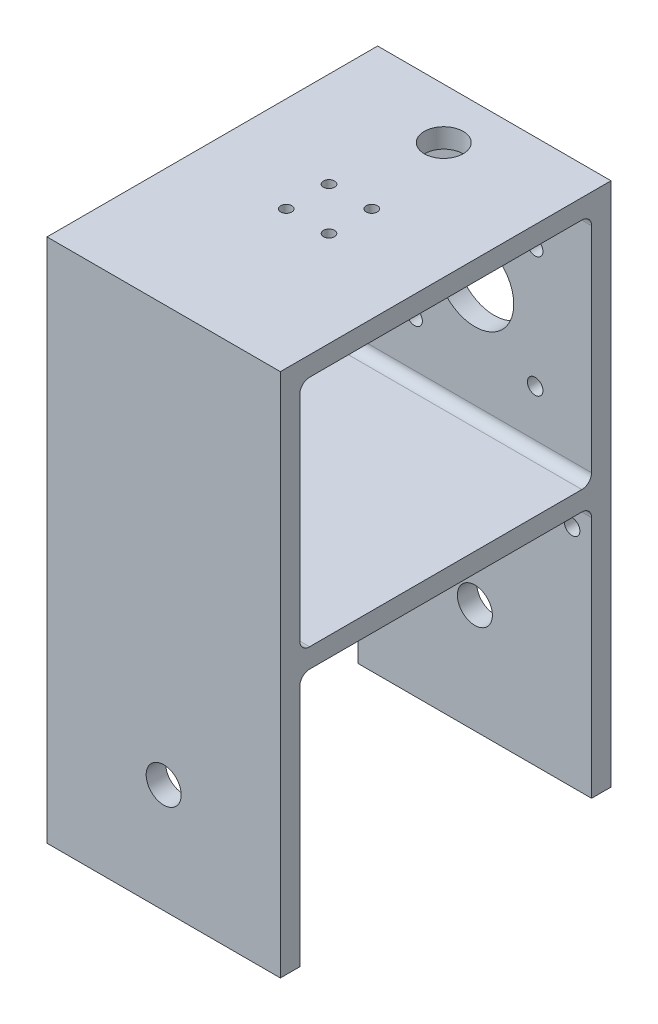
SolidWorks part; units mm, degrees
ref_plane "Front Plane" through (0, 0, 0) normal (0, 0, 1) x (1, 0, 0)
ref_plane "Top Plane" through (0, 0, 0) normal (0, 1, 0) x (1, 0, 0)
ref_plane "Right Plane" through (0, 0, 0) normal (1, 0, 0) x (0, 0, -1)
sketch "Sketch1" plane through (0, 0, 0) normal (1, 0, 0) x (0, 0, -1)
  line L0 (0, 0) -> (0, -135)
  line L1 (0, -135) -> (-5, -135)
  line L2 (-5, -135) -> (-5, -70)
  line L3 (-5, -70) -> (-80, -70)
  line L4 (-80, -70) -> (-80, -135)
  line L5 (-80, -135) -> (-85, -135)
  line L6 (-85, -135) -> (-85, 0)
  line L7 (-85, 0) -> (0, 0)
  dimension "D1" = 85
  dimension "D2" = 5
  dimension "D3" = 5
  dimension "D4" = 75
  dimension "D5" = 65
  dimension "D6" = 65
  dimension "D7" = 70
  dimension "D8" = 135
extrude "Boss-Extrude1" add sketch "Sketch1" against normal blind 60
sketch "Sketch2" plane through (0, 0, 0) normal (1, 0, 0) x (0, 0, -1)
  line L0 (-80, -70) -> (-5, -70) construction
  line L1 (-80, -65) -> (-5, -65)
  line L2 (-80, -65) -> (-80, -5)
  line L3 (-80, -5) -> (-5, -5)
  line L4 (-5, -65) -> (-5, -5)
  line L5 (0, 0) -> (-85, 0) construction
  line L6 (0, -135) -> (0, 0) construction
  line L7 (-85, 0) -> (-85, -135) construction
  dimension "D1" = 5
  dimension "D2" = 5
  dimension "D3" = 5
  dimension "D4" = 5
  dimension "D5" = 60
extrude "Cut-Extrude1" cut sketch "Sketch2" against normal blind 60
sketch "Sketch3" plane through (0, 0, 0) normal (0, 1, 0) x (1, 0, 0)
  line L0 (-30, 0) -> (-30, -85) construction
  line L1 (-60, 0) -> (0, 0) construction
  line L2 (-60, -85) -> (0, -85) construction
  line L3 (-60, -42.5) -> (0, -42.5) construction
  line L4 (-60, 0) -> (-60, -85) construction
  line L5 (0, 0) -> (0, -85) construction
  circle A0 centre (-35.5, -37) radius 1.425
  circle A1 centre (-24.5, -37) radius 1.425
  circle A2 centre (-24.5, -48) radius 1.425
  circle A3 centre (-35.5, -48) radius 1.425
  circle A4 centre (-30, -13) radius 5
  dimension "D5" = 2.85
  dimension "D6" = 2.85
  dimension "D7" = 2.85
  dimension "D8" = 2.85
  dimension "D9" = 10
  dimension "D1" = 11
  dimension "D2" = 11
  dimension "D3" = 24.5
  dimension "D4" = 37
  dimension "D10" = 13
extrude "Cut-Extrude2" cut sketch "Sketch3" against normal up to next
sketch "Sketch4" plane through (0, 0, 0) normal (0, 0, 1) x (1, 0, 0)
  line L0 (-30, 0) -> (-30, -135) construction
  line L1 (-60, 0) -> (0, 0) construction
  line L2 (-60, -135) -> (0, -135) construction
  line L3 (-60, 0) -> (0, 0) construction
  line L4 (0, 0) -> (0, -135) construction
  line L5 (-60, 0) -> (-60, -135) construction
  line L6 (-60, -135) -> (0, -135) construction
  line L11 (0, -67.5) -> (-60, -67.5) construction
  line L12 (0, -135) -> (0, 0) construction
  line L13 (-60, -135) -> (-60, 0) construction
  circle A0 centre (-30, -107) radius 4.5
  circle A1 centre (-30, -35) radius 10
  circle A6 centre (-5, -77) radius 2
  circle A7 centre (-55, -77) radius 2
  circle A8 centre (-14.5, -19.5) radius 2
  circle A9 centre (-45.5, -19.5) radius 2
  circle A10 centre (-45.5, -50.5) radius 2
  circle A11 centre (-14.5, -50.5) radius 2
  dimension "D2" = 9
  dimension "D3" = 20
  dimension "D7" = 4
  dimension "D8" = 4
  dimension "D9" = 4
  dimension "D10" = 4
  dimension "D19" = 4
  dimension "D20" = 4
  dimension "D4" = 72
  dimension "D5" = 31
  dimension "D6" = 31
  dimension "D11" = 19.5
  dimension "D12" = 17
  dimension "D13" = 9.5
  dimension "D14" = 9.5
  dimension "D15" = 28
  dimension "D16" = 58
  dimension "D17" = 5
  dimension "D18" = 5
  dimension "D21" = 58
extrude "Cut-Extrude3" cut sketch "Sketch4" along normal up to next
fillet "Fillet1" radius 2.5 1 edges at (-30, -70, 80)
fillet "Fillet2" radius 2.5 1 edges at (-30, -70, 5)
fillet "Fillet3" radius 2.5 1 edges at (-30, -65, 80)
fillet "Fillet4" radius 2.5 1 edges at (-30, -65, 5)
fillet "Fillet5" radius 2.5 1 edges at (-30, -5, 5)
fillet "Fillet6" radius 2.5 1 edges at (-30, -5, 80)
sketch "Sketch5" plane through (0, 0, 85) normal (0, 0, 1) x (1, 0, 0)
  line L0 (-30, 0) -> (-30, -135) construction
  line L1 (-60, 0) -> (0, 0) construction
  line L2 (-60, -135) -> (0, -135) construction
  circle A0 centre (-30, -107) radius 4.5
  dimension "D2" = 9
  dimension "D1" = 28
extrude "Cut-Extrude4" cut sketch "Sketch5" against normal up to next
